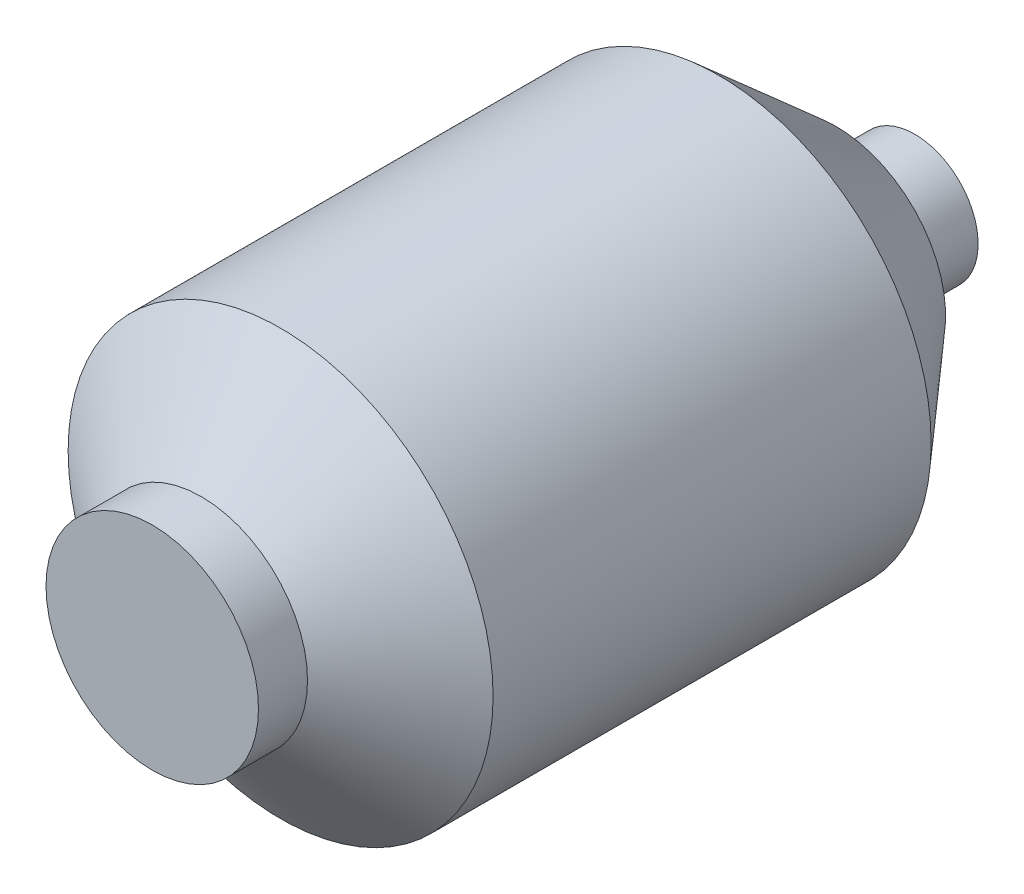
SolidWorks part; units mm, degrees
ref_plane "Front Plane" through (0, 0, 0) normal (0, 0, 1) x (1, 0, 0)
ref_plane "Top Plane" through (0, 0, 0) normal (0, 1, 0) x (1, 0, 0)
ref_plane "Right Plane" through (0, 0, 0) normal (1, 0, 0) x (0, 0, -1)
sketch "Sketch1" plane through (0, 0, 0) normal (0, 1, 0) x (1, 0, 0)
  line L0 (0, 73.0837) -> (0, -80.6494) construction
  line L1 (-33.4819, 44.0509) -> (-65, 8.1169)
  line L2 (-65, 8.1169) -> (-65, -125.8831)
  line L3 (-65, -125.8831) -> (-32.5, -150.1531)
  line L5 (0, -150.1531) -> (0, 68.1169)
  line L6 (0, 68.1169) -> (-19.3735, 68.1169)
  line L7 (-19.3735, 68.1169) -> (-19.3735, 46.8469)
  line L8 (-19.3735, 46.8469) -> (-33.4819, 44.0509)
  line L9 (-32.5, -150.1531) -> (-32.5, -165.1531)
  line L10 (-32.5, -165.1531) -> (0, -165.1531)
  line L11 (0, -165.1531) -> (0, -150.1531)
  dimension "D1" = 20
  dimension "D2" = 197
  dimension "D3" = 15
  dimension "D5" = 32.5
  dimension "D6" = 65
  dimension "D7" = 21.27
revolve "Revolve1" add sketch "Sketch1" angle 360 about L0
